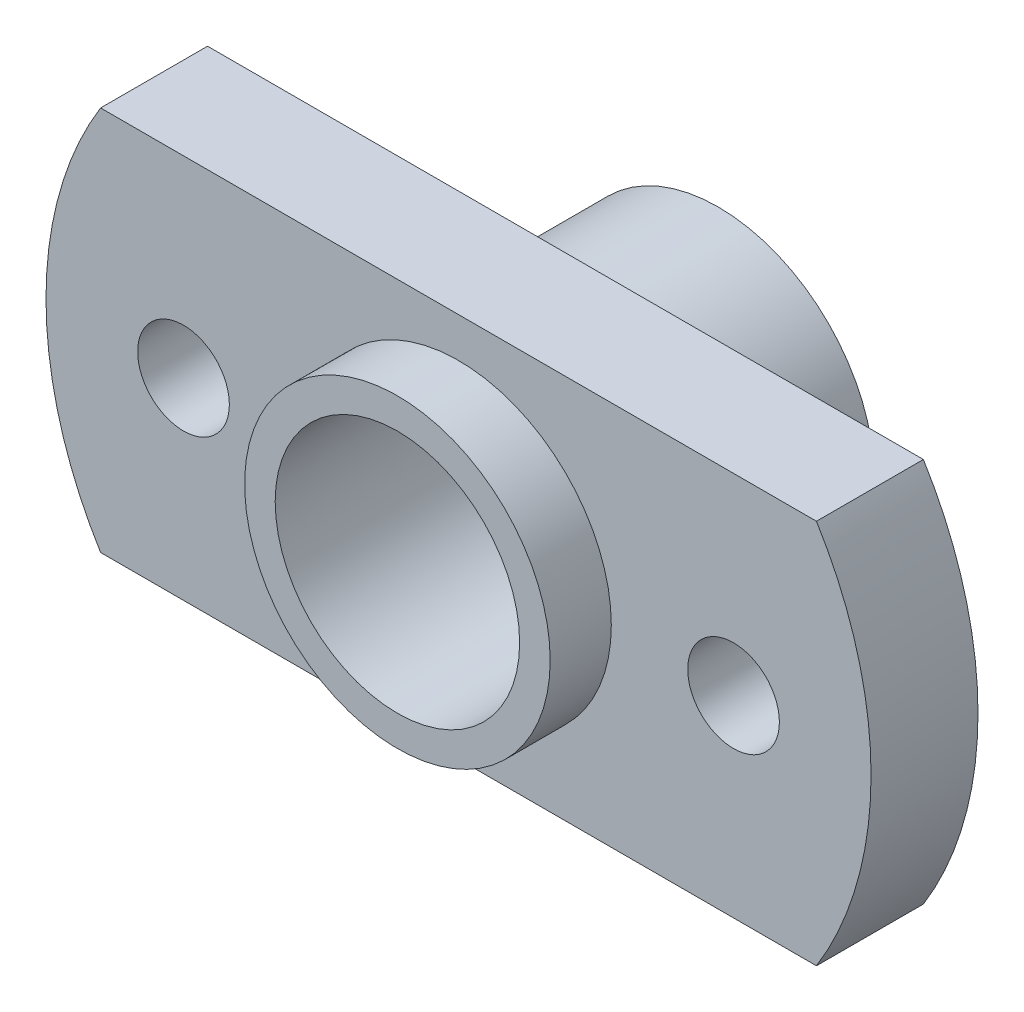
SolidWorks part; units mm, degrees
ref_plane "Front Plane" through (0, 0, 0) normal (0, 0, 1) x (1, 0, 0)
ref_plane "Top Plane" through (0, 0, 0) normal (0, 1, 0) x (1, 0, 0)
ref_plane "Right Plane" through (0, 0, 0) normal (1, 0, 0) x (0, 0, -1)
ref_plane "Plane1" through (0, 0, 177.0264) normal (0, 0, -1) x (-1, 0, 0)
sketch "Sketch1" plane through (0, 0, 177.0264) normal (0, 0, -1) x (-1, 0, 0)
  line L0 (177.8132, -74.2001) -> (154.3868, -74.2001)
  line L1 (154.3868, -86.8001) -> (177.8132, -86.8001)
  arc A0 (154.3868, -74.2001) -> (154.3868, -86.8001) centre (164.6, -80.5001) ccw
  arc A1 (177.8132, -86.8001) -> (177.8132, -74.2001) centre (167.6, -80.5001) ccw
extrude "Boss-Extrude1" add sketch "Sketch1" against normal blind 3.5
ref_plane "Plane2" through (0, -80.5001, 0) normal (0, 1, 0) x (1, 0, 0)
sketch "Sketch2" plane through (0, -80.5001, 0) normal (0, 1, 0) x (1, 0, 0)
  line L0 (-161.1, -180.5264) -> (-166.1, -180.5264)
  line L1 (-166.1, -180.5264) -> (-166.1, -182.5264)
  line L2 (-166.1, -182.5264) -> (-161.1, -182.5264)
  line L3 (-161.1, -182.5264) -> (-161.1, -180.5264)
  line L4 (-166.1, -180.5264) -> (-166.1, -182.5264) construction
revolve "Revolve1" add sketch "Sketch2" angle 360 about L4
ref_plane "Plane3" through (0, -80.5001, 0) normal (0, -1, 0) x (1, 0, 0)
sketch "Sketch3" plane through (0, -80.5001, 0) normal (0, -1, 0) x (1, 0, 0)
  line L0 (-161, 177.0264) -> (-166.1, 177.0264)
  line L1 (-166.1, 177.0264) -> (-166.1, 172.0264)
  line L2 (-166.1, 172.0264) -> (-161, 172.0264)
  line L3 (-161, 172.0264) -> (-161, 177.0264)
  line L4 (-166.1, 177.0264) -> (-166.1, 172.0264) construction
revolve "Revolve2" add sketch "Sketch3" angle 360 about L4
hole_wizard "Ø3.0 (3) Diameter Hole1" positions "Sketch5" profile "Sketch4" hole size "Ø3.0" standard "ANSI Metric"
sketch "Sketch5" plane through (0, 0, 180.5264) normal (0, 0, 1) x (1, 0, 0)
  point P0 (-157.1, -80.5001)
  point P1 (-175.1, -80.5001)
sketch "Sketch4" plane through (-157.1, -80.5001, 180.5264) normal (1, 0, 0) x (0, -1, 0)
  line L0 (0, 0) -> (0, 8.5)
  line L1 (0, 8.5) -> (1.5, 8.5)
  line L2 (1.5, 8.5) -> (1.5, 0)
  line L5 (1.5, 0) -> (0, 0)
  line L11 (0, -6.35) -> (0, 107.95) construction
  dimension "Thru Hole Dia." = 3
  dimension "Thru Hole Depth" = 8.5
hole_wizard "Ø8.0 (8) Diameter Hole1" positions "Sketch7" profile "Sketch6" hole size "Ø8.0" standard "ANSI Metric"
sketch "Sketch7" plane through (0, 0, 172.0264) normal (0, 0, -1) x (-1, 0, 0)
  point P0 (166.1, -80.5001)
sketch "Sketch6" plane through (-166.1, -80.5001, 172.0264) normal (1, 0, 0) x (0, 1, 0)
  line L0 (0, 0) -> (0, 10.5)
  line L1 (0, 10.5) -> (4, 10.5)
  line L2 (4, 10.5) -> (4, 0)
  line L5 (4, 0) -> (0, 0)
  line L11 (0, -6.35) -> (0, 107.95) construction
  dimension "Thru Hole Dia." = 8
  dimension "Thru Hole Depth" = 10.5
